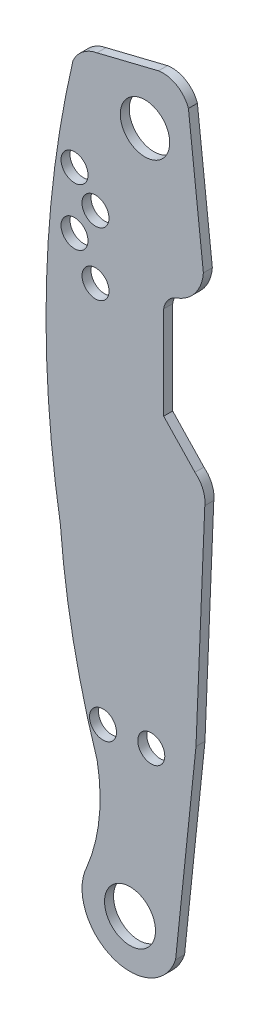
SolidWorks part; units mm, degrees
material "Plain Carbon Steel"
ref_plane "Front Plane" through (0, 0, 0) normal (0, 0, 1) x (1, 0, 0)
ref_plane "Top Plane" through (0, 0, 0) normal (0, 1, 0) x (1, 0, 0)
ref_plane "Right Plane" through (0, 0, 0) normal (1, 0, 0) x (0, 0, -1)
sketch "Sketch1" plane through (0, 0, 0) normal (0, 0, 1) x (1, 0, 0)
  line L0 (19.9436, 44.8731) -> (99.7179, 44.8731) construction
  line L1 (74.0095, 2.5248) -> (72.282, -13.9852)
  line L2 (74.7574, 20.5588) -> (74.0095, 2.5248)
  line L3 (71.2749, 25.3848) -> (73.9224, 22.5908)
  line L4 (71.2749, 33.2588) -> (71.2749, 25.3848)
  line L7 (73.3708, 49.0068) -> (74.6351, 37.5768)
  line L8 (65.6275, 49.2142) -> (70.8345, 50.4988)
  arc A0 (63.5896, 47.6177) -> (62.5268, 13.052) centre (149.7015, 27.6708) ccw
  arc A1 (62.5268, 13.052) -> (65.6358, -2.6564) centre (130.1435, 18.2728) ccw
  arc A3 (64.7664, -10.9388) -> (72.282, -13.9852) centre (68.4215, -12.7152) ccw
  arc A5 (74.7574, 20.5588) -> (73.9224, 22.5908) centre (72.4855, 20.8128) ccw
  arc A7 (71.2749, 33.2588) -> (72.3798, 34.6055) centre (72.9576, 33.0048) cw
  arc A8 (72.3798, 34.6055) -> (74.6351, 37.5768) centre (71.2155, 37.8308) ccw
  arc A12 (63.5896, 47.6177) -> (65.6275, 49.2142) centre (66.1355, 46.4668) cw
  circle A13 centre (68.4215, -12.7152) radius 2.159
  circle A14 centre (70.2249, 0.4928) radius 1.143
  circle A15 centre (66.1355, 0.2028) radius 1.143
  circle A16 centre (65.5005, 32.2428) radius 1.143
  circle A17 centre (65.5005, 37.5768) radius 1.143
  circle A18 centre (69.6915, 45.7048) radius 2.0955
  circle A19 centre (63.7225, 39.8628) radius 1.143
  circle A20 centre (63.7225, 35.0368) radius 1.143
  circle A21 centre (68.4215, -12.7152) radius 3.683 construction
  arc A22 (70.8345, 50.4988) -> (73.3708, 49.0068) centre (71.2155, 48.2448) cw
  arc A25 (65.6358, -2.6564) -> (64.7664, -10.9388) centre (51.4035, -5.3492) cw
  point P7 (0, 0)
  point P15 (0, 0)
  dimension "D1" = 1.524
  dimension "D2" = 4.191
  dimension "D3" = 2.54
  dimension "D4" = 2.286
  dimension "D5" = 7.874
  dimension "D6" = 1.524
  dimension "D7" = 3.429
  dimension "D8" = 3.556
  dimension "D10" = 2.794
  dimension "D11" = 1.143
  dimension "D12" = 4.064
  dimension "D13" = 3.302
  dimension "D19" = 2.286
  dimension "D20" = 20.32
  dimension "D9" = 0.762
  dimension "D23" = 43.18
  dimension "D26" = 59.69
  dimension "D29" = 4.064
  dimension "D32" = 18.288
  dimension "D36" = 27.432
  dimension "D24" = 4.318
  dimension "D43" = 10.668
  dimension "D45" = 8.128
  dimension "D17" = 24.892
  dimension "D16" = 1.7018
  dimension "D30" = 4.318
  dimension "D33" = 14.4848
  dimension "D38" = 88.392
  dimension "D39" = 67.818
  dimension "D40" = 2.286
  dimension "D41" = 5.842
  dimension "D51" = 2.286
  dimension "D14" = 8.128
  dimension "D15" = 12.7
  dimension "D18" = 2.794
  dimension "D21" = 12.446
  dimension "D22" = 23.114
  dimension "D25" = 25.146
  dimension "D27" = 58.42
  dimension "D28" = 1.27
  dimension "D31" = 51.054
  dimension "D34" = 80.01
  dimension "D35" = 60.452
  dimension "D37" = 18.034
  dimension "D42" = 5.969
  dimension "D44" = 45.502
  dimension "D46" = 4.191
  dimension "D47" = 13.462
  dimension "D48" = 45.212
  dimension "D49" = 0.5334
  dimension "D50" = 3.556
extrude "Boss-Extrude1" add sketch "Sketch1" along normal mid plane 0.762
